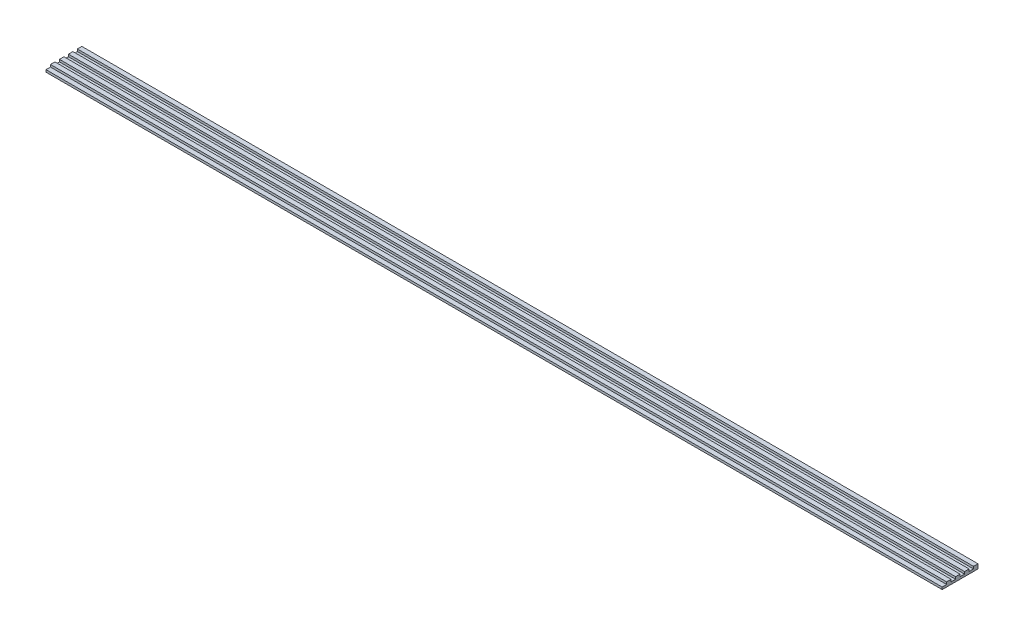
SolidWorks part; units mm, degrees
ref_plane "Front Plane" through (0, 0, 0) normal (0, 0, 1) x (1, 0, 0)
ref_plane "Top Plane" through (0, 0, 0) normal (0, 1, 0) x (1, 0, 0)
ref_plane "Right Plane" through (0, 0, 0) normal (1, 0, 0) x (0, 0, -1)
sketch "Sketch1" plane through (0, 0, 0) normal (0, 1, 0) x (1, 0, 0)
  line L1 (-100, 4) -> (100, 4)
  line L2 (-100, 4) -> (-100, -4)
  line L3 (-100, -4) -> (100, -4)
  line L4 (100, 4) -> (100, -4)
  line L5 (-100, 4) -> (100, -4) construction
  line L6 (-100, -4) -> (100, 4) construction
  point P0 (0, 0)
  dimension "D1" = 200
  dimension "D2" = 8
extrude "Boss-Extrude1" add sketch "Sketch1" along normal blind 0.5
sketch "Sketch2" plane through (0, 0.5, 0) normal (0, 1, 0) x (1, 0, 0)
  line L0 (100, -4) -> (100, 4) construction
  line L1 (-100, 4) -> (100, 4)
  line L2 (-100, 4) -> (-100, 3)
  line L3 (-100, 3) -> (100, 3)
  line L4 (100, 4) -> (100, 3)
  line L13 (-100, 2) -> (-100, 1)
  line L14 (-100, 2) -> (100, 2)
  line L15 (100, 2) -> (100, 1)
  line L16 (-100, 1) -> (100, 1)
  line L17 (-100, 0) -> (-100, -1)
  line L18 (-100, 0) -> (100, 0)
  line L19 (100, 0) -> (100, -1)
  line L20 (-100, -1) -> (100, -1)
  line L21 (-100, -2) -> (-100, -3)
  line L22 (-100, -2) -> (100, -2)
  line L23 (100, -2) -> (100, -3)
  line L24 (-100, -3) -> (100, -3)
  dimension "D1" = 1
  dimension "D2" = 4
extrude "Boss-Extrude2" add sketch "Sketch2" along normal blind 0.5
